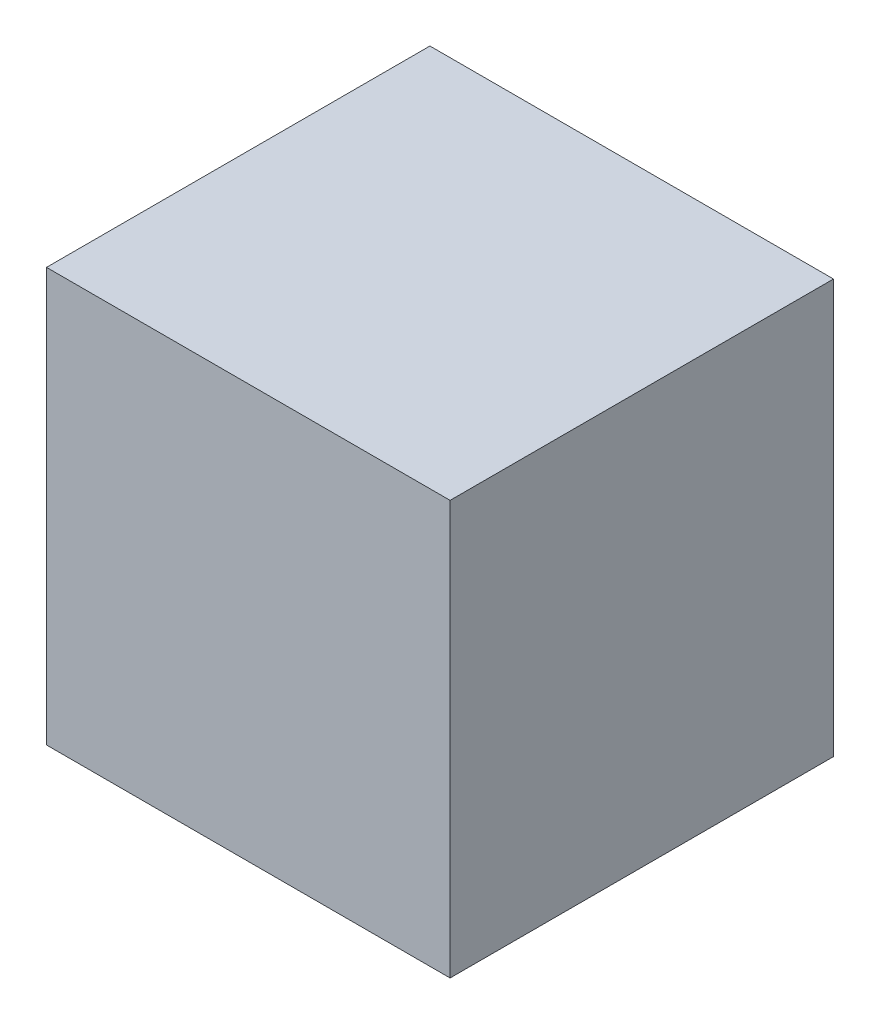
SolidWorks part; units mm, degrees
ref_plane "Front Plane" through (0, 0, 0) normal (0, 0, 1) x (1, 0, 0)
ref_plane "Top Plane" through (0, 0, 0) normal (0, 1, 0) x (1, 0, 0)
ref_plane "Right Plane" through (0, 0, 0) normal (1, 0, 0) x (0, 0, -1)
sketch "Sketch1" plane through (0, 0, 0) normal (0, 1, 0) x (1, 0, 0)
  line L1 (-20, -19) -> (20, -19)
  line L2 (-20, -19) -> (-20, 19)
  line L3 (-20, 19) -> (20, 19)
  line L4 (20, -19) -> (20, 19)
  line L5 (-20, -19) -> (20, 19) construction
  line L6 (-20, 19) -> (20, -19) construction
  point P0 (0, 0)
  dimension "D1" = 40
  dimension "D2" = 38
extrude "Boss-Extrude1" add sketch "Sketch1" along normal blind 41 contours L2 L1 L4 L3
